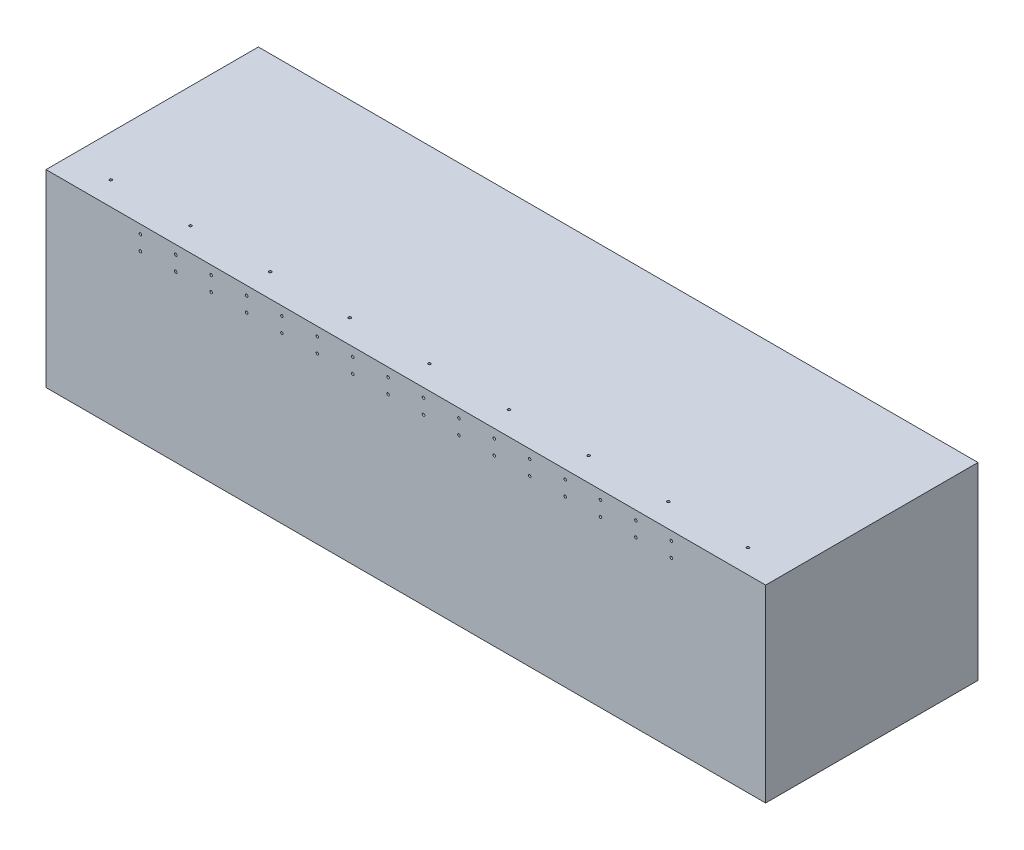
SolidWorks part; units mm, degrees
material "SolidB"
ref_plane "Front Plane" through (0, 0, 0) normal (0, 0, 1) x (1, 0, 0)
ref_plane "Top Plane" through (0, 0, 0) normal (0, 1, 0) x (1, 0, 0)
ref_plane "Right Plane" through (0, 0, 0) normal (1, 0, 0) x (0, 0, -1)
sketch "Sketch1" plane through (0, 0, 0) normal (0, 1, 0) x (1, 0, 0)
  line L1 (0, 0) -> (1549.4, 0)
  line L2 (0, 0) -> (0, 457.2)
  line L3 (0, 457.2) -> (1549.4, 457.2)
  line L4 (1549.4, 0) -> (1549.4, 457.2)
  dimension "D1" = 457.2
  dimension "D2" = 1549.4
extrude "Boss-Extrude1" add sketch "Sketch1" against normal blind 406.4
sketch "Sketch2" plane through (0, 0, 0) normal (0, 0, 1) x (1, 0, 0)
  line L4 (0, 0) -> (1549.4, 0) construction
  line L5 (774.7, 0) -> (774.7, -406.4) construction
  line L6 (0, -406.4) -> (1549.4, -406.4) construction
  line L9 (203.2, -19.05) -> (1346.2, -19.05) construction
  line L10 (203.2, -50.8) -> (1346.2, -50.8) construction
  point P20 (774.7, -19.05)
  dimension "D5" = 1143
  dimension "D6" = 19.05
  dimension "D7" = 31.75
sketch "Sketch6" plane through (0, 0, -457.2) normal (0, 0, -1) x (-1, 0, 0)
  line L0 (-774.7, 0) -> (-774.7, -406.4) construction
  line L1 (-15.875, -25.4) -> (-15.875, -76.2) construction
  line L2 (-15.875, -76.2) -> (-15.875, -127) construction
  line L3 (0, -406.4) -> (0, 0) construction
  line L4 (-1549.4, 0) -> (0, 0) construction
  line L5 (-1533.525, -76.2) -> (-1533.525, -127) construction
  line L6 (-1533.525, -25.4) -> (-1533.525, -76.2) construction
  dimension "D1" = 50.8
  dimension "D2" = 50.8
  dimension "D3" = 15.875
  dimension "D4" = 25.4
hole_wizard "Hole1" positions "3DSketch1" profile "Sketch3" legacy
sketch3d "3DSketch1"
  point P7 (15.875, -25.4, -457.2)
  point P10 (1533.525, -25.4, -457.2)
sketch "Sketch3" plane through (15.875, -25.4, -457.2) normal (1, 0, 0) x (0, 1, 0)
  line L0 (0, 0) -> (0, 5.08)
  line L1 (0, 5.08) -> (2.794, 5.08)
  line L2 (2.794, 5.08) -> (2.794, 0)
  line L3 (2.794, 0) -> (0, 0)
  line L4 (0, 110) -> (0, -10) construction
  dimension "Diameter" = 5.588
  dimension "Depth" = 5.08
pattern_linear "LPattern1" count 3 spacing 50.8 along (0, -1, 0) of "Hole1"
hole_wizard "Hole2" positions "3DSketch2" profile "Sketch4" legacy
sketch3d "3DSketch2"
  point P0 (203.2, -19.05, 0)
  point P3 (203.2, -50.8, 0)
sketch "Sketch4" plane through (203.2, -19.05, 0) normal (1, 0, 0) x (0, -1, 0)
  line L0 (0, 0) -> (0, 5.08)
  line L1 (0, 5.08) -> (2.794, 5.08)
  line L2 (2.794, 5.08) -> (2.794, 0)
  line L3 (2.794, 0) -> (0, 0)
  line L4 (0, 110) -> (0, -10) construction
  dimension "Diameter" = 5.588
  dimension "Depth" = 5.08
pattern_linear "LPattern2" count 16 spacing 76.2 along (1, 0, 0) of "Hole2"
sketch "Sketch5" plane through (0, 0, 0) normal (0, 1, 0) x (1, 0, 0)
  line L0 (774.7, 0) -> (774.7, 457.2) construction
  line L1 (1549.4, 457.2) -> (0, 457.2) construction
sketch "Sketch7" plane through (0, 0, 0) normal (0, 1, 0) x (1, 0, 0)
  line L0 (774.7, 457.2) -> (774.7, 0) construction
  line L1 (0, 50.8) -> (1549.4, 50.8) construction
  line L2 (0, 457.2) -> (0, 0) construction
  line L3 (1549.4, 0) -> (1549.4, 457.2) construction
  line L4 (0, 0) -> (1549.4, 0) construction
  point P14 (88.9, 50.8)
  dimension "D1" = 50.8
  dimension "D2" = 88.9
hole_wizard "Hole3" positions "3DSketch3" profile "Sketch8" legacy
sketch3d "3DSketch3"
  point P0 (88.9, 0, -50.8)
sketch "Sketch8" plane through (88.9, 0, -50.8) normal (1, 0, 0) x (0, 0, 1)
  line L0 (0, 0) -> (0, 5.08)
  line L1 (0, 5.08) -> (2.794, 5.08)
  line L2 (2.794, 5.08) -> (2.794, 0)
  line L3 (2.794, 0) -> (0, 0)
  line L4 (0, 110) -> (0, -10) construction
  dimension "Diameter" = 5.588
  dimension "Depth" = 5.08
pattern_linear "LPattern3" count 9 spacing 171.45 along (1, 0, 0) of "Hole3"
